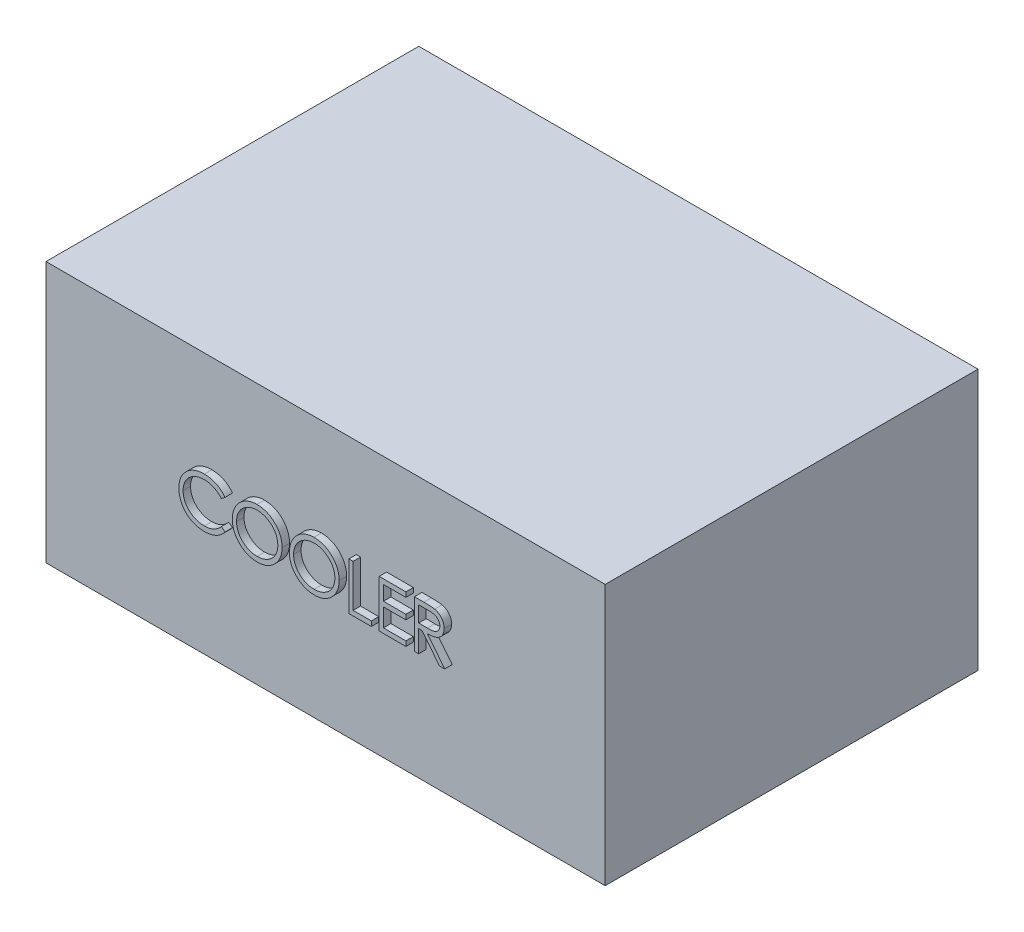
SolidWorks part; units mm, degrees
ref_plane "정면" through (0, 0, 0) normal (0, 0, 1) x (1, 0, 0)
ref_plane "윗면" through (0, 0, 0) normal (0, 1, 0) x (1, 0, 0)
ref_plane "우측면" through (0, 0, 0) normal (1, 0, 0) x (0, 0, -1)
sketch "스케치1" plane through (0, 0, 0) normal (0, 0, 1) x (1, 0, 0)
  line L1 (0, 0) -> (150, 0)
  line L2 (0, 0) -> (0, -70)
  line L3 (0, -70) -> (150, -70)
  line L4 (150, 0) -> (150, -70)
  dimension "D1" = 150
  dimension "D2" = 70
extrude "보스-돌출1" add sketch "스케치1" along normal blind 100
sketch "스케치2" plane through (0, 0, 100) normal (0, 0, 1) x (1, 0, 0)
  text T0 "COOLER" font "Century Gothic" height in points 48
extrude "보스-돌출2" add sketch "스케치2" along normal blind 2
